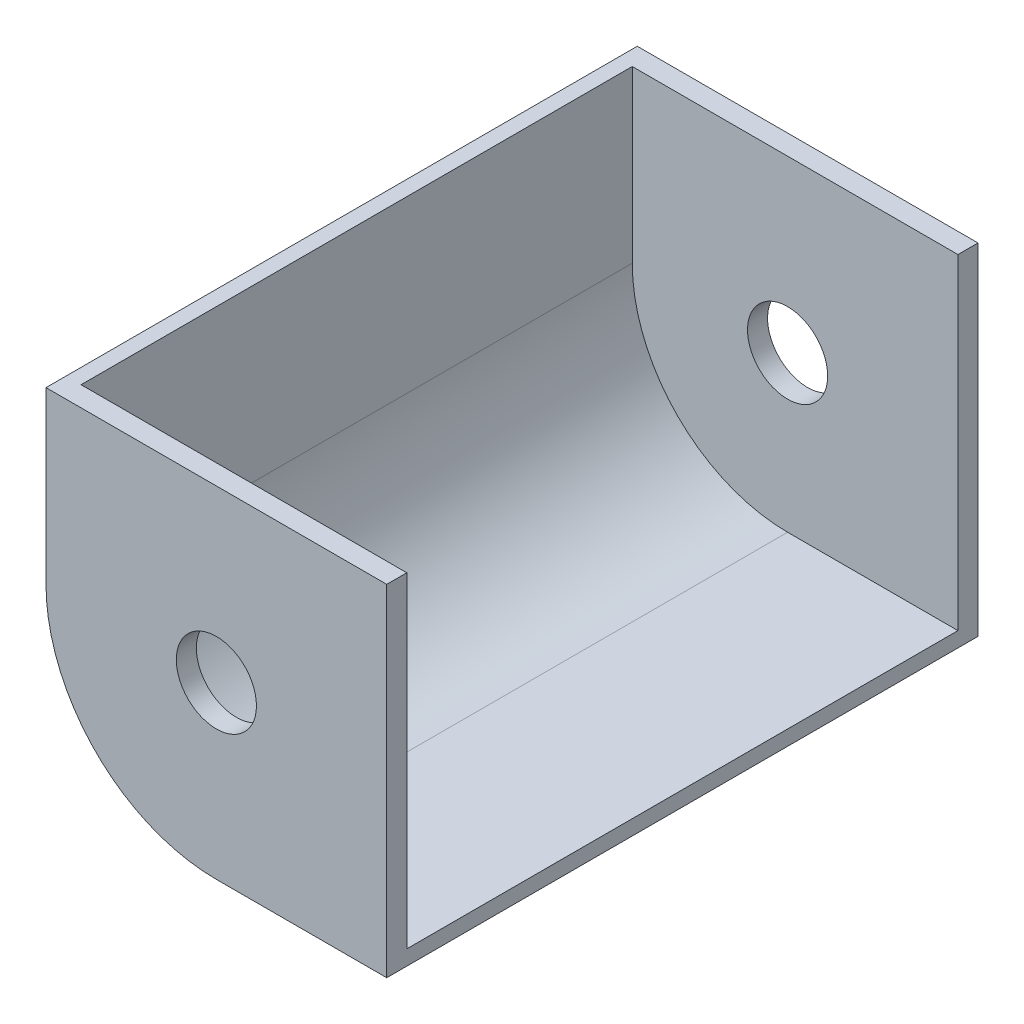
SolidWorks part; units mm, degrees
ref_plane "Front Plane" through (0, 0, 0) normal (0, 0, 1) x (1, 0, 0)
ref_plane "Top Plane" through (0, 0, 0) normal (0, 1, 0) x (1, 0, 0)
ref_plane "Right Plane" through (0, 0, 0) normal (1, 0, 0) x (0, 0, -1)
sketch "Sketch1" plane through (0, 0, 0) normal (0, 0, 1) x (1, 0, 0)
  line L0 (-17, 0) -> (0, 0)
  line L1 (0, 17) -> (0, 0)
  line L2 (0, 17) -> (0, 34)
  line L3 (0, 34) -> (-17, 34)
  line L4 (-34, 17) -> (-34, 34)
  line L5 (-34, 34) -> (-17, 34)
  arc A0 (-34, 17) -> (-17, 0) centre (-17, 17) ccw
  dimension "D1" = 17
  dimension "D2" = 34
  dimension "D3" = 34
extrude "Boss-Extrude1" add sketch "Sketch1" along normal blind 2
sketch "Sketch2" plane through (0, 0, 2) normal (0, 0, 1) x (1, 0, 0)
  line L0 (-17, 0) -> (0, 0) construction
  line L1 (-34, 34) -> (-34, 17) construction
  line L2 (-17, 0) -> (0, 0)
  line L3 (-34, 34) -> (-34, 17)
  line L4 (-32.5, 34) -> (-32.5, 17)
  line L5 (-17, 1.5) -> (0, 1.5)
  line L6 (-34, 34) -> (-32.5, 34)
  line L7 (0, 1.5) -> (0, 0)
  arc A0 (-34, 17) -> (-17, 0) centre (-17, 17) ccw construction
  arc A1 (-34, 17) -> (-17, 0) centre (-17, 17) ccw
  arc A2 (-32.5, 17) -> (-17, 1.5) centre (-17, 17) ccw
  dimension "D1" = 1.5
extrude "Boss-Extrude2" add sketch "Sketch2" along normal blind 55
sketch "Sketch3" plane through (0, 0, 57) normal (0, 0, 1) x (1, 0, 0)
  line L0 (0, 0) -> (0, 1.5) construction
  line L1 (-32.5, 34) -> (-34, 34) construction
  line L2 (0, 34) -> (-32.5, 34) construction
  line L3 (0, 1.5) -> (0, 34) construction
  line L4 (-17, 0) -> (0, 0) construction
  line L5 (-34, 34) -> (-34, 17) construction
  line L6 (0, 0) -> (0, 1.5)
  line L7 (-32.5, 34) -> (-34, 34)
  line L8 (0, 34) -> (-32.5, 34)
  line L9 (0, 1.5) -> (0, 34)
  line L10 (-17, 0) -> (0, 0)
  line L11 (-34, 34) -> (-34, 17)
  arc A0 (-34, 17) -> (-17, 0) centre (-17, 17) ccw construction
  arc A1 (-34, 17) -> (-17, 0) centre (-17, 17) ccw
extrude "Boss-Extrude3" add sketch "Sketch3" along normal blind 2
sketch "Sketch4" plane through (0, 0, 59) normal (0, 0, 1) x (1, 0, 0)
  circle A0 centre (-17, 17) radius 4
  dimension "D1" = 8
extrude "Cut-Extrude1" cut sketch "Sketch4" against normal through all
